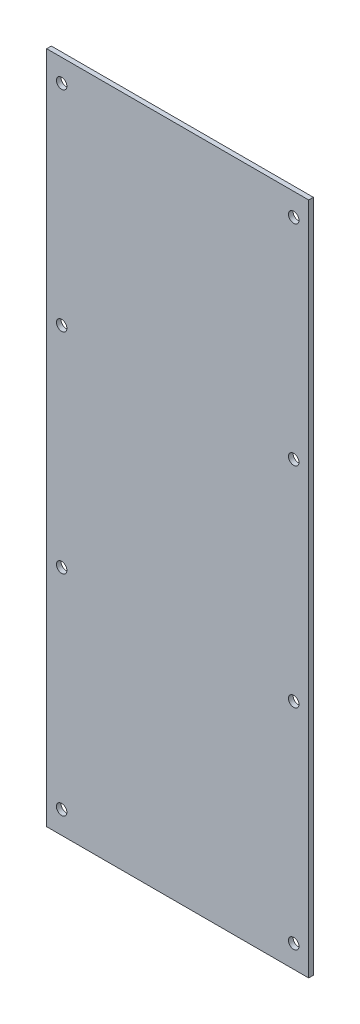
SolidWorks part; units mm, degrees
ref_plane "Front" through (0, 0, 0) normal (0, 0, 1) x (1, 0, 0)
ref_plane "Top" through (0, 0, 0) normal (0, 1, 0) x (1, 0, 0)
ref_plane "Right" through (0, 0, 0) normal (1, 0, 0) x (0, 0, -1)
sketch "Sketch1" plane through (0, 0, 0) normal (0, 0, 1) x (1, 0, 0)
  line L1 (0, 0) -> (88.9, 0)
  line L2 (0, 0) -> (0, -228.6)
  line L3 (0, -228.6) -> (88.9, -228.6)
  line L4 (88.9, 0) -> (88.9, -228.6)
  dimension "D1" = 88.9
  dimension "D2" = 228.6
extrude "Extrude1" add sketch "Sketch1" along normal blind 1.5748
sketch "Sketch2" plane through (0, 0, 1.5748) normal (0, 0, 1) x (1, 0, 0)
  line L0 (88.9, 0) -> (0, 0) construction
  line L1 (0, 0) -> (0, -228.6) construction
  circle A0 centre (5.08, -7.62) radius 1.778
  dimension "D1" = 7.62
  dimension "D2" = 3.556
  dimension "D3" = 5.08
extrude "Cut-Extrude1" cut sketch "Sketch2" against normal blind 2.54
pattern_linear "LPattern1" count 2 spacing 78.74 count 4 spacing 71.12
